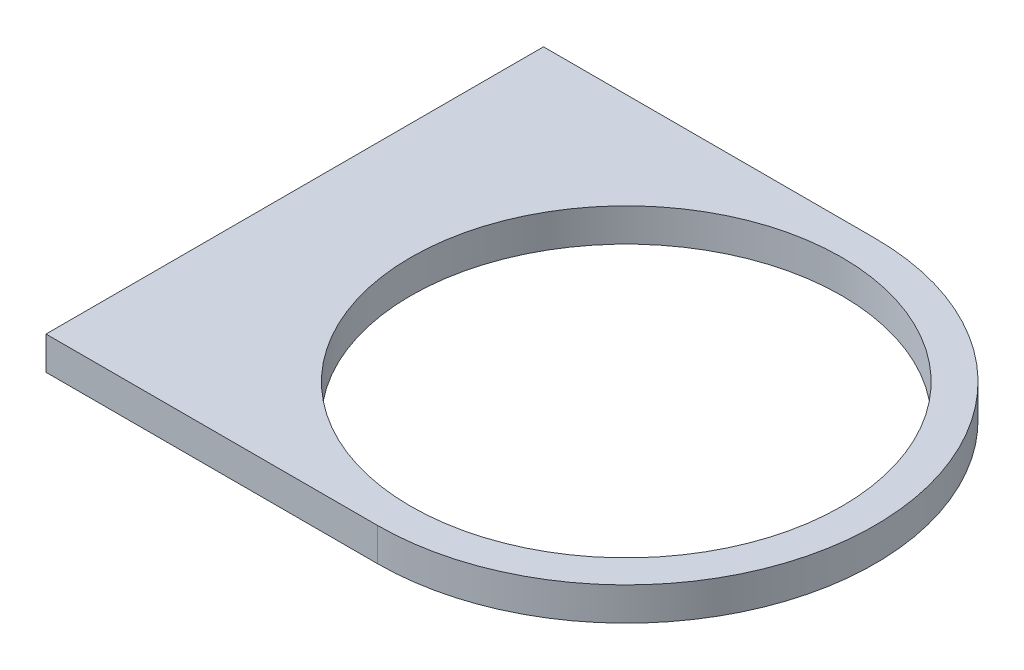
SolidWorks part; units mm, degrees
ref_plane "Front Plane" through (0, 0, 0) normal (0, 0, 1) x (1, 0, 0)
ref_plane "Top Plane" through (0, 0, 0) normal (0, 1, 0) x (1, 0, 0)
ref_plane "Right Plane" through (0, 0, 0) normal (1, 0, 0) x (0, 0, -1)
sketch "Sketch1" plane through (0, 0, 0) normal (0, 0, 1) x (1, 0, 0)
  line L0 (0, 0) -> (36.6665, 419.1) construction
  line L1 (36.6665, 419.1) -> (155.7226, 419.1) construction
  line L2 (155.7226, 419.1) -> (155.7226, 0) construction
  line L3 (155.7226, 0) -> (0, 0) construction
  line L4 (155.7226, -1000) -> (155.7226, 49000) construction
  line L5 (1.8042, 20.6221) -> (36.6665, 419.1) construction
  line L6 (1.8042, 20.6221) -> (41.652, 17.1359) construction
  line L7 (36.6665, 419.1) -> (76.5143, 415.6138) construction
  line L8 (41.652, 17.1359) -> (76.5143, 415.6138) construction
  line L9 (60.4726, -1000) -> (60.4726, 49000) construction
  line L10 (-52.7184, 317.5) -> (-128.6284, 324.1413) construction
  line L11 (-30.1965, 414.3375) -> (36.6601, 414.3375) construction
  line L12 (-1162.1335, 304.8) -> (48837.8665, 304.8) construction
  line L13 (-130.0274, 292.1) -> (-53.8274, 292.1) construction
  line L14 (-128.6284, 324.1413) -> (-53.8274, 292.1) construction
  line L15 (-52.7184, 317.5) -> (-130.0274, 292.1) construction
  line L16 (36.6601, 338.1375) -> (-30.1965, 338.1375) construction
  line L17 (-138.1172, 324.9714) -> (27.1662, 310.511)
  line L18 (-138.1172, 324.9714) -> (-137.5638, 331.2973)
  line L19 (-137.5638, 331.2973) -> (36.6665, 419.1)
  line L20 (36.6665, 419.1) -> (104.9226, 419.1)
  line L21 (104.9226, 419.1) -> (104.9226, 0) construction
  line L22 (27.1662, 310.511) -> (0.3389, 3.8741)
  line L23 (0.3389, 3.8741) -> (44.6198, 0)
  line L24 (44.6198, 0) -> (104.9226, 0)
  line L25 (104.9226, 419.1) -> (155.7226, 311.15)
  line L26 (155.7226, 311.15) -> (155.7226, 304.8)
  line L27 (155.7226, 304.8) -> (104.9226, 280.8941)
  line L28 (104.9226, 280.8941) -> (104.9226, 0)
  arc A0 (-128.6284, 324.1413) -> (-30.1965, 414.3375) centre (-30.1965, 315.5296) cw construction
  arc A1 (69.9976, 304.8) -> (36.6601, 338.1375) centre (36.6601, 304.8) ccw construction
  arc A2 (146.1976, 304.8) -> (36.6601, 414.3375) centre (36.6601, 304.8) ccw construction
  arc A3 (-52.7184, 317.5) -> (-30.1965, 338.1375) centre (-30.1965, 315.5296) cw construction
  point P7 (54.1226, 400.05)
  point P17 (146.1976, 304.8)
  point P18 (69.9976, 304.8)
  dimension "D9" = 9.525
  dimension "D14" = 25.4
  dimension "D1" = 419.1
  dimension "D2" = 101.6
  dimension "D3" = 19.05
  dimension "D4" = 19.05
  dimension "D5" = 85
  dimension "D6" = 40
  dimension "D7" = 400
  dimension "D8" = 95.25
  dimension "D10" = 9.525
  dimension "D11" = 114.3
  dimension "D12" = 76.2
  dimension "D13" = 9.525
  dimension "D15" = 127
  dimension "D16" = 9.525
  dimension "D17" = 209.55
  dimension "D18" = 6.35
  dimension "D19" = 50.8
  dimension "D20" = 44.45
  dimension "D21" = 6.35
sketch "Sketch2" plane through (0, 0, 0) normal (0, 0, 1) x (1, 0, 0)
  line L1 (155.7226, 0) -> (44.6198, 0)
  line L2 (155.7226, 0) -> (155.7226, 6.35)
  line L3 (155.7226, 6.35) -> (44.6198, 6.35)
  line L4 (44.6198, 0) -> (44.6198, 6.35)
  dimension "D1" = 6.35
extrude "Boss-Extrude1" add sketch "Sketch2" along normal blind 95.25
sketch "Sketch3" plane through (0, 6.35, 0) normal (0, 1, 0) x (1, 0, 0)
  line L0 (155.7226, -47.625) -> (108.0976, -47.625) construction
  line L1 (155.7226, -95.25) -> (155.7226, 0) construction
  circle A0 centre (108.0976, -47.625) radius 41.275
  dimension "D1" = 82.55
  dimension "D2" = 47.625
extrude "Cut-Extrude2" cut sketch "Sketch3" against normal through all
sketch "Sketch4" plane through (0, 6.35, 0) normal (0, 1, 0) x (1, 0, 0)
  line L0 (155.7226, -95.25) -> (44.6198, -95.25) construction
  line L1 (-201162.1335, 0) -> (248837.8665, 0) construction
  line L2 (108.0976, -95.25) -> (179.0514, -95.25)
  line L3 (179.0514, -95.25) -> (179.0514, 0)
  line L4 (179.0514, 0) -> (108.0976, 0)
  arc A0 (108.0976, -95.25) -> (108.0976, 0) centre (108.0976, -47.625) ccw
extrude "Cut-Extrude3" cut sketch "Sketch4" against normal through all
